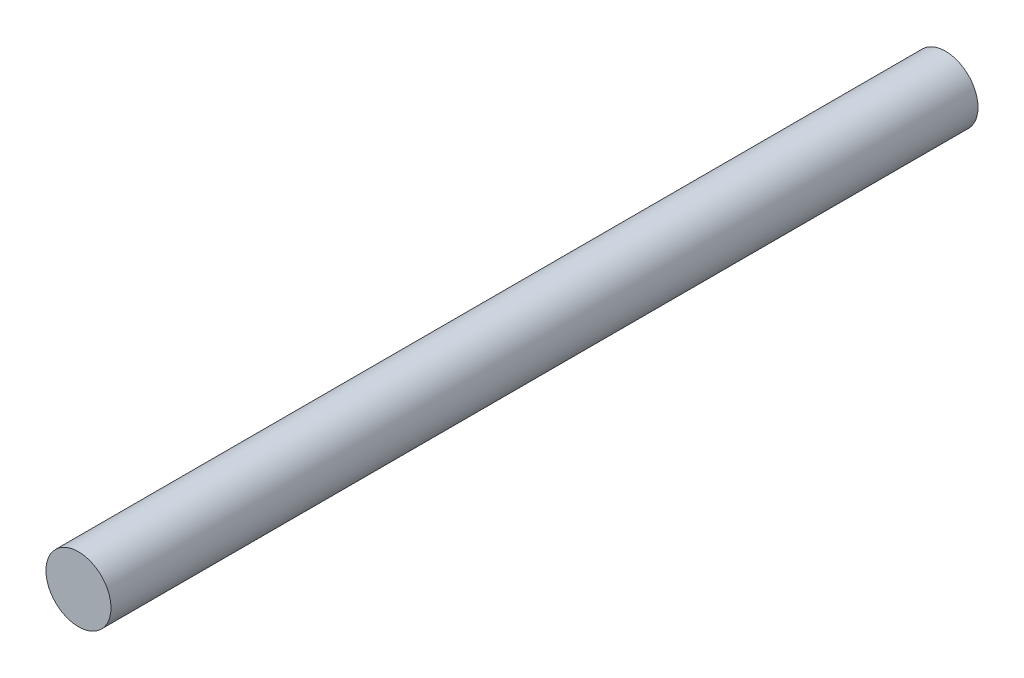
SolidWorks part; units mm, degrees
material "6063-T6"
ref_plane "Front Plane" through (0, 0, 0) normal (0, 0, 1) x (1, 0, 0)
ref_plane "Top Plane" through (0, 0, 0) normal (0, 1, 0) x (1, 0, 0)
ref_plane "Right Plane" through (0, 0, 0) normal (1, 0, 0) x (0, 0, -1)
sketch "Sketch1" plane through (0, 0, 0) normal (0, 0, 1) x (1, 0, 0)
  circle A0 centre (0, 0) radius 1.5
  dimension "D1" = 3
extrude "Boss-Extrude1" add sketch "Sketch1" along normal blind 40
